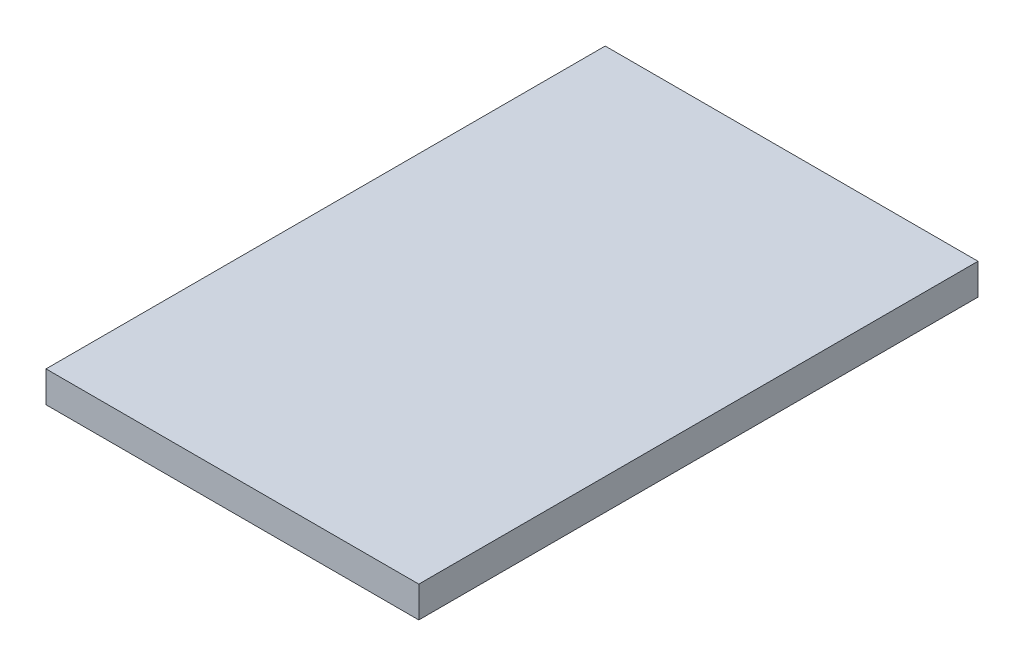
SolidWorks part; units mm, degrees
ref_plane "Front Plane" through (0, 0, 0) normal (0, 0, 1) x (1, 0, 0)
ref_plane "Top Plane" through (0, 0, 0) normal (0, 1, 0) x (1, 0, 0)
ref_plane "Right Plane" through (0, 0, 0) normal (1, 0, 0) x (0, 0, -1)
sketch "Sketch1" plane through (0, 0, 0) normal (0, 0, 1) x (1, 0, 0)
  line L1 (-152.4, -12.7) -> (152.4, -12.7)
  line L2 (-152.4, -12.7) -> (-152.4, 12.7)
  line L3 (-152.4, 12.7) -> (152.4, 12.7)
  line L4 (152.4, -12.7) -> (152.4, 12.7)
  line L5 (-152.4, -12.7) -> (152.4, 12.7) construction
  line L6 (-152.4, 12.7) -> (152.4, -12.7) construction
  point P0 (0, 0)
  dimension "D1" = 304.8
  dimension "D2" = 25.4
extrude "Boss-Extrude1" add sketch "Sketch1" along normal blind 457.2
